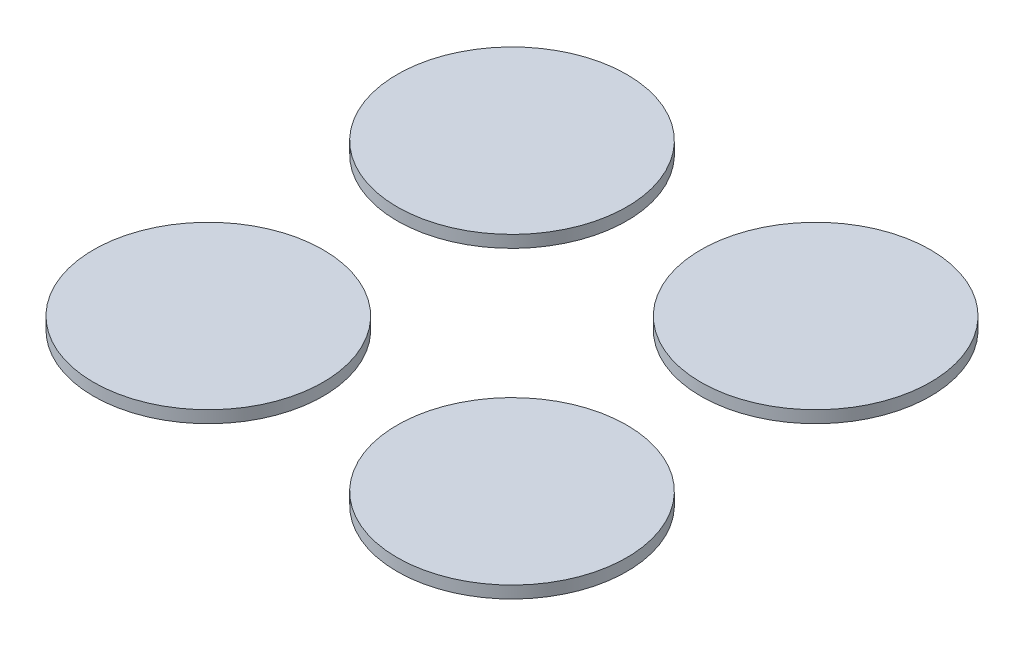
SolidWorks part; units mm, degrees
ref_plane "Front Plane" through (0, 0, 0) normal (0, 0, 1) x (1, 0, 0)
ref_plane "Top Plane" through (0, 0, 0) normal (0, 1, 0) x (1, 0, 0)
ref_plane "Right Plane" through (0, 0, 0) normal (1, 0, 0) x (0, 0, -1)
sketch "Sketch1" plane through (0, 0, 0) normal (0, 1, 0) x (1, 0, 0)
  circle A0 centre (-30.445, 30.445) radius 23.02
  circle A1 centre (30.445, 30.445) radius 23.02
  circle A2 centre (30.445, -30.445) radius 23.02
  circle A3 centre (-30.445, -30.445) radius 23.02
  circle A4 centre (-30.445, 30.445) radius 2.96 construction
  circle A5 centre (30.445, -30.445) radius 2.96 construction
  point P15 (0, 0)
  dimension "D1" = 4
  dimension "D2" = 46.04
extrude "Boss-Extrude1" add sketch "Sketch1" along normal blind 2.43
